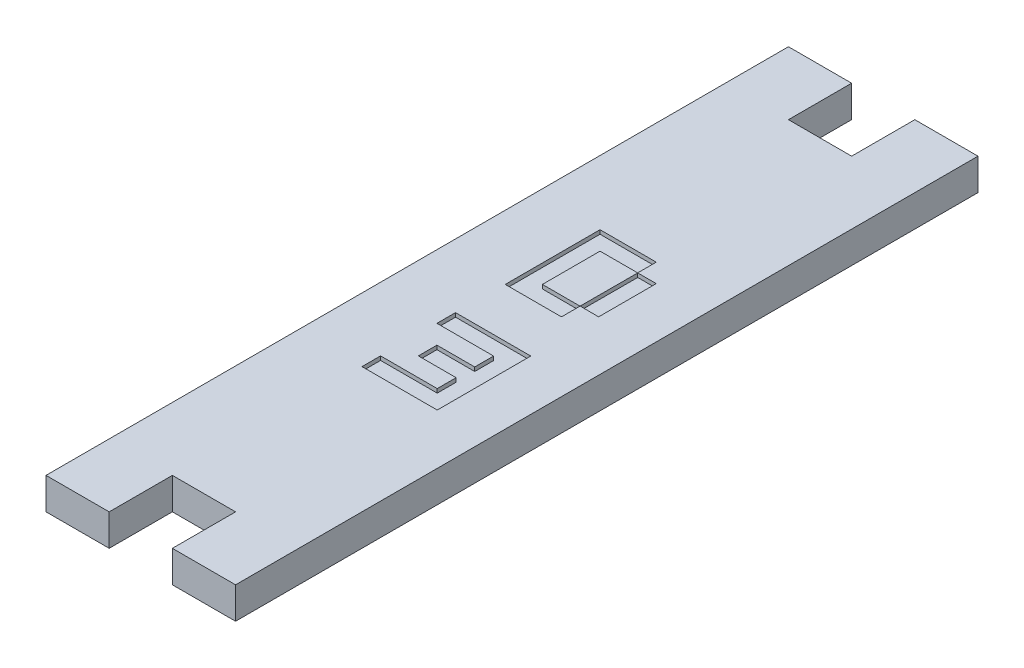
SolidWorks part; units mm, degrees
ref_plane "前基準面" through (0, 0, 0) normal (0, 0, 1) x (1, 0, 0)
ref_plane "上基準面" through (0, 0, 0) normal (0, 1, 0) x (1, 0, 0)
ref_plane "右基準面" through (0, 0, 0) normal (1, 0, 0) x (0, 0, -1)
ref_plane "平面1" through (0, 4, 0) normal (0, 1, 0) x (1, 0, 0)
sketch "草圖1" plane through (0, 4, 0) normal (0, 1, 0) x (1, 0, 0)
  line L0 (12, 47) -> (-12, 47)
  line L1 (-12, 47) -> (-12, -47)
  line L2 (-12, -47) -> (12, -47)
  line L3 (12, -47) -> (12, 47)
extrude "填料-伸長1" add sketch "草圖1" against normal blind 4
sketch "草圖2" plane through (0, 0, 0) normal (0, -1, 0) x (1, 0, 0)
  line L0 (-4, -47) -> (4, -47)
  line L1 (4, -47) -> (4, -39)
  line L2 (4, -39) -> (-4, -39)
  line L3 (-4, -39) -> (-4, -47)
extrude "除料-伸長1" cut sketch "草圖2" against normal through all
sketch "草圖3" plane through (0, 0, 0) normal (0, -1, 0) x (1, 0, 0)
  line L0 (4, 47) -> (-4, 47)
  line L1 (-4, 47) -> (-4, 39)
  line L2 (-4, 39) -> (4, 39)
  line L3 (4, 39) -> (4, 47)
extrude "除料-伸長2" cut sketch "草圖3" against normal through all
sketch "草圖4" plane through (0, 4, 0) normal (0, 1, 0) x (-1, 0, 0)
  line L0 (-5.6046, 15.0708) -> (-5.6046, 3.229)
  line L1 (-5.6046, 3.229) -> (3.922, 3.229)
  line L2 (3.922, 3.229) -> (3.922, 5.5816)
  line L3 (3.922, 5.5816) -> (-3.2521, 5.5816)
  line L4 (-3.2521, 5.5816) -> (-3.2521, 7.9736)
  line L5 (-3.2521, 7.9736) -> (1.5306, 7.9736)
  line L6 (1.5306, 7.9736) -> (1.5306, 10.3262)
  line L7 (1.5306, 10.3262) -> (-3.2521, 10.3262)
  line L8 (-3.2521, 10.3262) -> (-3.2521, 12.7183)
  line L9 (-3.2521, 12.7183) -> (3.922, 12.7183)
  line L10 (3.922, 12.7183) -> (3.922, 15.0708)
  line L11 (3.922, 15.0708) -> (-5.6046, 15.0708)
extrude "除料-伸長3" cut sketch "草圖4" against normal blind 0.5
sketch "草圖5" plane through (0, 4, 0) normal (0, 1, 0) x (-1, 0, 0)
  line L0 (1.5124, -5.3624) -> (1.5124, -12.6573)
  line L1 (1.5124, -12.6573) -> (-3.2521, -12.6573)
  line L2 (-3.2521, -12.6573) -> (-3.2521, -15.0099)
  line L3 (-3.2521, -15.0099) -> (3.8649, -15.0099)
  line L4 (3.8649, -15.0099) -> (3.8649, -3.0099)
  line L5 (3.8649, -3.0099) -> (-3.2521, -3.0099)
  line L6 (-3.2521, -3.0099) -> (-3.2521, -5.3624)
  line L7 (-3.2521, -5.3624) -> (1.5124, -5.3624)
extrude "除料-伸長4" cut sketch "草圖5" against normal blind 0.5
sketch "草圖6" plane through (0, 4, 0) normal (0, 1, 0) x (-1, 0, 0)
  line L0 (-5.6046, -12.6573) -> (-3.2621, -12.6573)
  line L1 (-3.2621, -12.6573) -> (-3.2521, -5.3724)
  line L2 (-3.2521, -5.3724) -> (-5.6046, -5.3624)
  line L3 (-5.6046, -5.3624) -> (-5.6046, -12.6573)
extrude "除料-伸長5" cut sketch "草圖6" against normal blind 0.5
